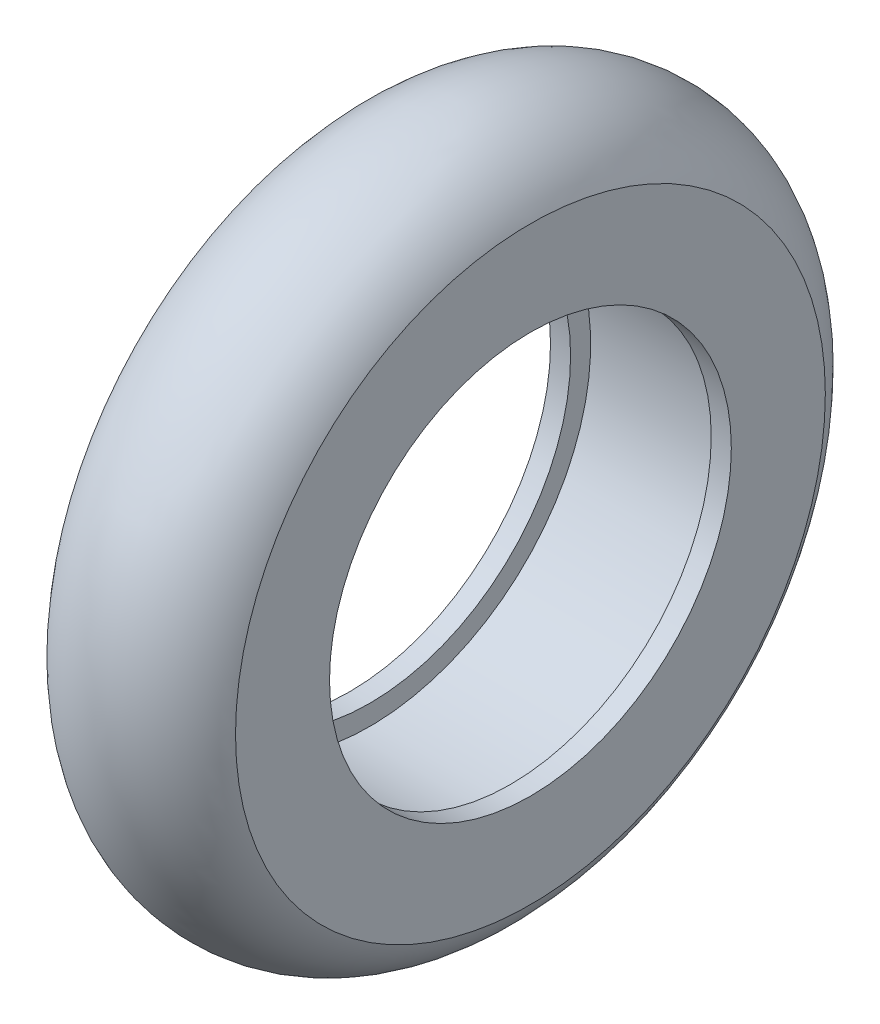
SolidWorks part; units mm, degrees
ref_plane "Front Plane" through (0, 0, 0) normal (0, 0, 1) x (1, 0, 0)
ref_plane "Top Plane" through (0, 0, 0) normal (0, 1, 0) x (1, 0, 0)
ref_plane "Right Plane" through (0, 0, 0) normal (1, 0, 0) x (0, 0, -1)
sketch "Sketch1" plane through (0, 0, 0) normal (0, 0, 1) x (1, 0, 0)
  line L0 (-8, 10) -> (-9, 10)
  line L1 (-9, 10) -> (-9, 14.6794)
  line L3 (0, 14.6794) -> (0, 10)
  line L4 (0, 10) -> (-1, 10)
  line L5 (-1, 10) -> (-1, 11)
  line L6 (-1, 11) -> (-8, 11)
  line L7 (-8, 11) -> (-8, 10)
  line L8 (-4.5, 0) -> (-4.5, 17.5) construction
  line L9 (-9, 0) -> (0, 0) construction
  arc A0 (0, 14.6794) -> (-9, 14.6794) centre (-4.5, 12.5) ccw
  dimension "MSM_4" = 22
  dimension "R" = 5
  dimension "MSM_1" = 1
  dimension "MSM_3" = 1
  dimension "MSM_2" = 1
  dimension "D" = 35
  dimension "B" = 9
revolve "Revolve1" add sketch "Sketch1" angle 360 about L9
